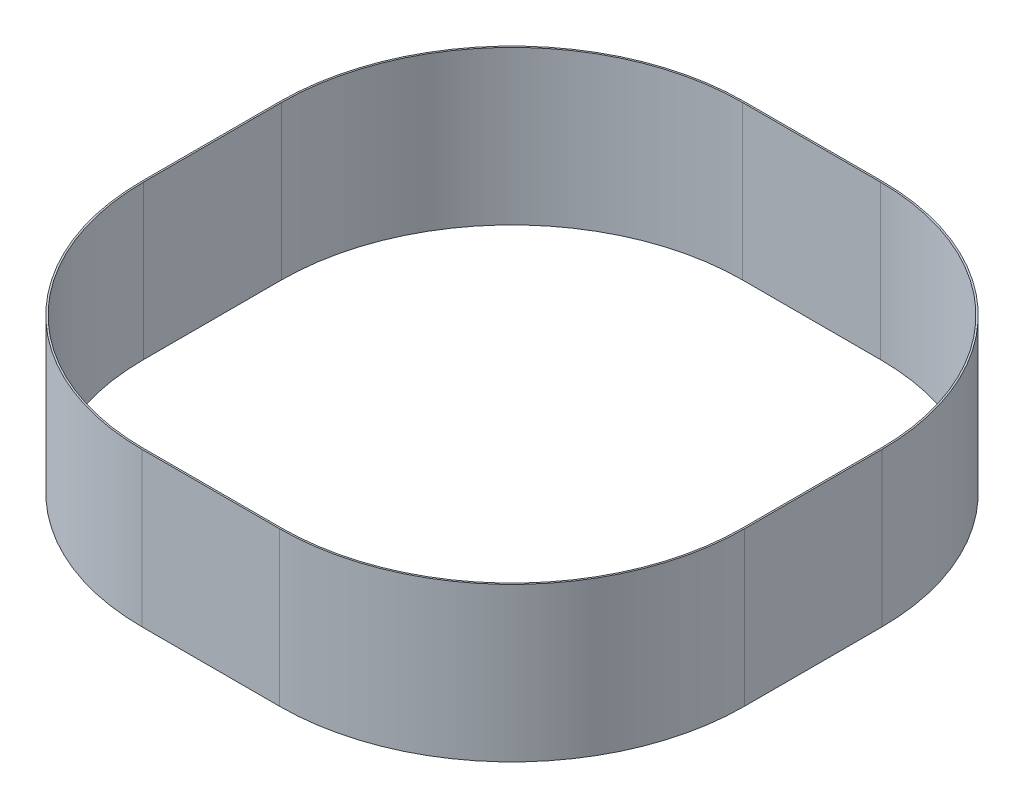
SolidWorks part; units mm, degrees
ref_plane "Front Plane" through (0, 0, 0) normal (0, 0, 1) x (1, 0, 0)
ref_plane "Top Plane" through (0, 0, 0) normal (0, 1, 0) x (1, 0, 0)
ref_plane "Right Plane" through (0, 0, 0) normal (1, 0, 0) x (0, 0, -1)
sketch "Sketch1" plane through (0, 0, 0) normal (0, 1, 0) x (1, 0, 0)
  line L0 (-34.1312, 149.225) -> (34.1313, 149.225)
  line L1 (-34.1312, -148.4312) -> (34.1312, -148.4312)
  line L2 (-148.4312, -34.1312) -> (-148.4312, 34.1312)
  line L3 (-34.1312, 148.4312) -> (34.1312, 148.4312)
  line L4 (148.4313, -34.1312) -> (148.4313, 34.1312)
  line L5 (-148.4312, -148.4312) -> (148.4313, 148.4312) construction
  line L6 (-148.4312, 148.4312) -> (148.4313, -148.4312) construction
  line L7 (149.225, -34.1312) -> (149.225, 34.1312)
  line L8 (-34.1312, -149.225) -> (34.1312, -149.225)
  line L9 (-149.225, -34.1312) -> (-149.225, 34.1313)
  arc A0 (-34.1312, -148.4312) -> (-148.4312, -34.1312) centre (-34.1312, -34.1313) cw
  arc A1 (34.1312, -148.4312) -> (148.4313, -34.1312) centre (34.1313, -34.1312) ccw
  arc A2 (34.1312, 148.4312) -> (148.4313, 34.1312) centre (34.1313, 34.1313) cw
  arc A3 (-148.4312, 34.1312) -> (-34.1312, 148.4312) centre (-34.1312, 34.1312) cw
  arc A4 (-149.225, 34.1313) -> (-34.1312, 149.225) centre (-34.1312, 34.1312) cw
  arc A5 (34.1313, 149.225) -> (149.225, 34.1312) centre (34.1313, 34.1313) cw
  arc A6 (34.1312, -149.225) -> (149.225, -34.1312) centre (34.1313, -34.1312) ccw
  arc A7 (-34.1312, -149.225) -> (-149.225, -34.1312) centre (-34.1312, -34.1313) cw
  point P0 (0, 0)
  dimension "D3" = 114.3
  dimension "D1" = 296.8625
  dimension "D2" = 296.8625
  dimension "D4" = 0.7937
extrude "Boss-Extrude1" add sketch "Sketch1" along normal blind 76.2
